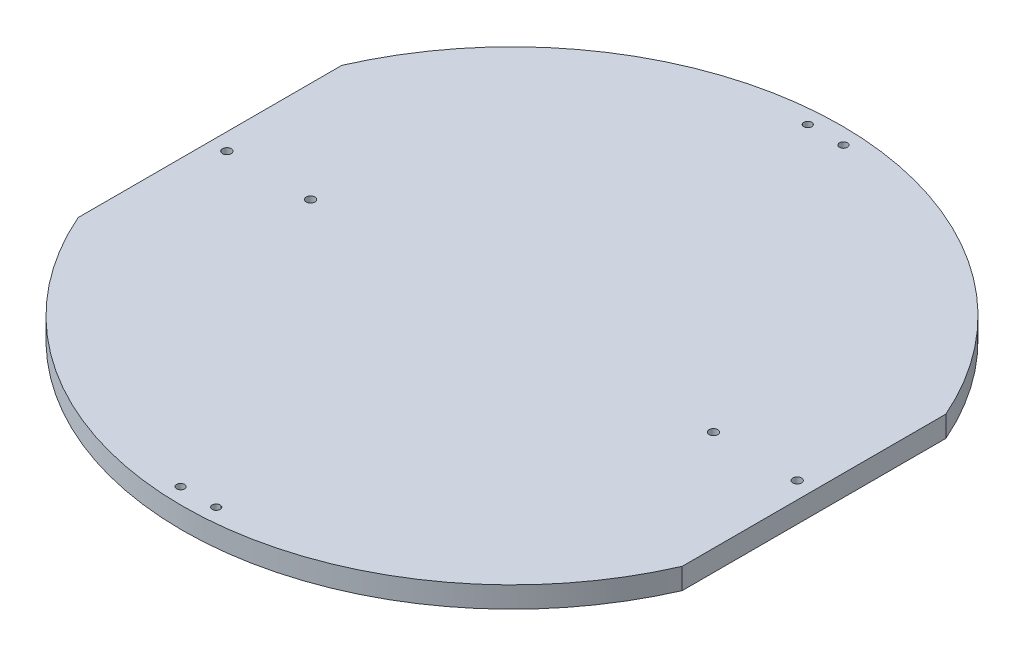
SolidWorks part; units mm, degrees
ref_plane "Alzado" through (0, 0, 0) normal (0, 0, 1) x (1, 0, 0)
ref_plane "Planta" through (0, 0, 0) normal (0, 1, 0) x (1, 0, 0)
ref_plane "Vista lateral" through (0, 0, 0) normal (1, 0, 0) x (0, 0, -1)
sketch "Croquis1" plane through (0, 0, 0) normal (0, 1, 0) x (1, 0, 0)
  line L0 (-114.5644, 0) -> (114.5644, 0) construction
  line L2 (-114.5644, -50) -> (-114.5644, 50)
  line L4 (114.5644, -50) -> (114.5644, 50)
  line L5 (0, -55) -> (0, 55) construction
  line L6 (0, 125) -> (0, -125) construction
  arc A0 (114.5644, 50) -> (-114.5644, 50) centre (0, 0) ccw
  arc A1 (-114.5644, -50) -> (114.5644, -50) centre (0, 0) ccw
  circle A2 centre (108.1644, 0) radius 1.65
  circle A3 centre (76.4144, 0) radius 1.65
  circle A4 centre (-108.1644, 0) radius 1.65
  circle A5 centre (-76.4144, 0) radius 1.65
  circle A6 centre (-6.75, 118.95) radius 1.5
  circle A7 centre (6.75, 118.95) radius 1.5
  circle A8 centre (6.75, -118.95) radius 1.5
  circle A9 centre (-6.75, -118.95) radius 1.5
  dimension "D1" = 250
  dimension "D5" = 3.3
  dimension "D6" = 3.3
  dimension "D8" = 3
  dimension "D2" = 100
  dimension "D3" = 100
  dimension "D4" = 6.4
  dimension "D7" = 31.75
  dimension "D9" = 6.75
  dimension "D10" = 6.05
extrude "Saliente-Extruir1" add sketch "Croquis1" along normal blind 8
